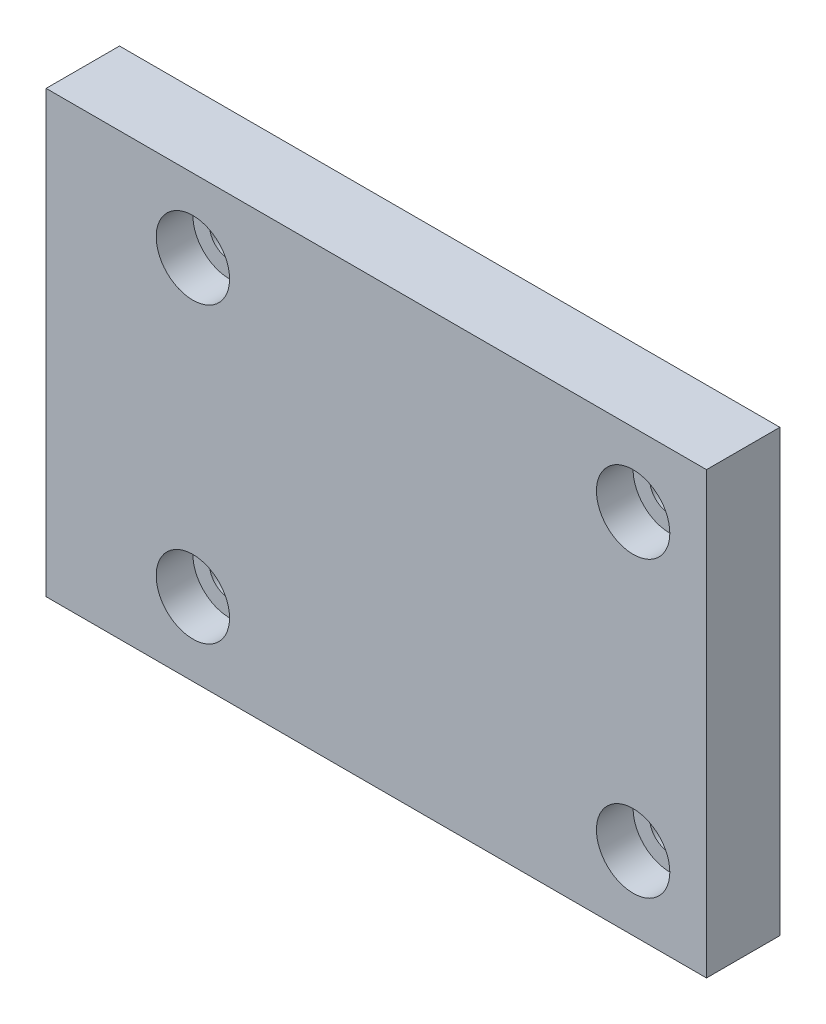
SolidWorks part; units mm, degrees
ref_plane "Front Plane" through (0, 0, 0) normal (0, 0, 1) x (1, 0, 0)
ref_plane "Top Plane" through (0, 0, 0) normal (0, 1, 0) x (1, 0, 0)
ref_plane "Right Plane" through (0, 0, 0) normal (1, 0, 0) x (0, 0, -1)
sketch "Sketch1" plane through (0, 0, 0) normal (0, 0, 1) x (1, 0, 0)
  line L1 (-45, -30) -> (45, -30)
  line L2 (-45, -30) -> (-45, 30)
  line L3 (-45, 30) -> (45, 30)
  line L4 (45, -30) -> (45, 30)
  line L5 (-45, -30) -> (45, 30) construction
  line L6 (-45, 30) -> (45, -30) construction
  point P0 (0, 0)
  dimension "D1" = 90
  dimension "D2" = 60
extrude "Boss-Extrude1" add sketch "Sketch1" along normal mid plane 10
hole_wizard "CBORE for M5 SHCS1" positions "Sketch2" profile "Sketch3" counterbore size "M5" standard "ANSI Metric" end condition through all
sketch "Sketch2" plane through (0, 0, 5) normal (0, 0, 1) x (1, 0, 0)
  line L0 (-45, 30) -> (-45, -30) construction
  line L1 (45, 30) -> (-45, 30) construction
  point P0 (-25, 20)
  dimension "D1" = 20
  dimension "D2" = 10
sketch "Sketch3" plane through (-25, 20, 5) normal (1, 0, 0) x (0, -1, 0)
  line L0 (0, 0) -> (0, 10)
  line L1 (0, 10) -> (2.75, 10)
  line L3 (2.75, 10) -> (2.75, 5)
  line L4 (2.75, 5) -> (5, 5)
  line L5 (5, 5) -> (5, 0)
  line L7 (5, 0) -> (0, 0)
  line L11 (0, -6.35) -> (0, 107.95) construction
  dimension "Thru Hole Dia." = 5.5
  dimension "Thru Hole Depth" = 10
  dimension "C'Bore Dia." = 10
  dimension "C'Bore Depth" = 5
pattern_linear "LPattern1" count 2 spacing 60 along (1, 0, 0) count 2 spacing 40 along (0, -1, 0) of "CBORE for M5 SHCS1"
